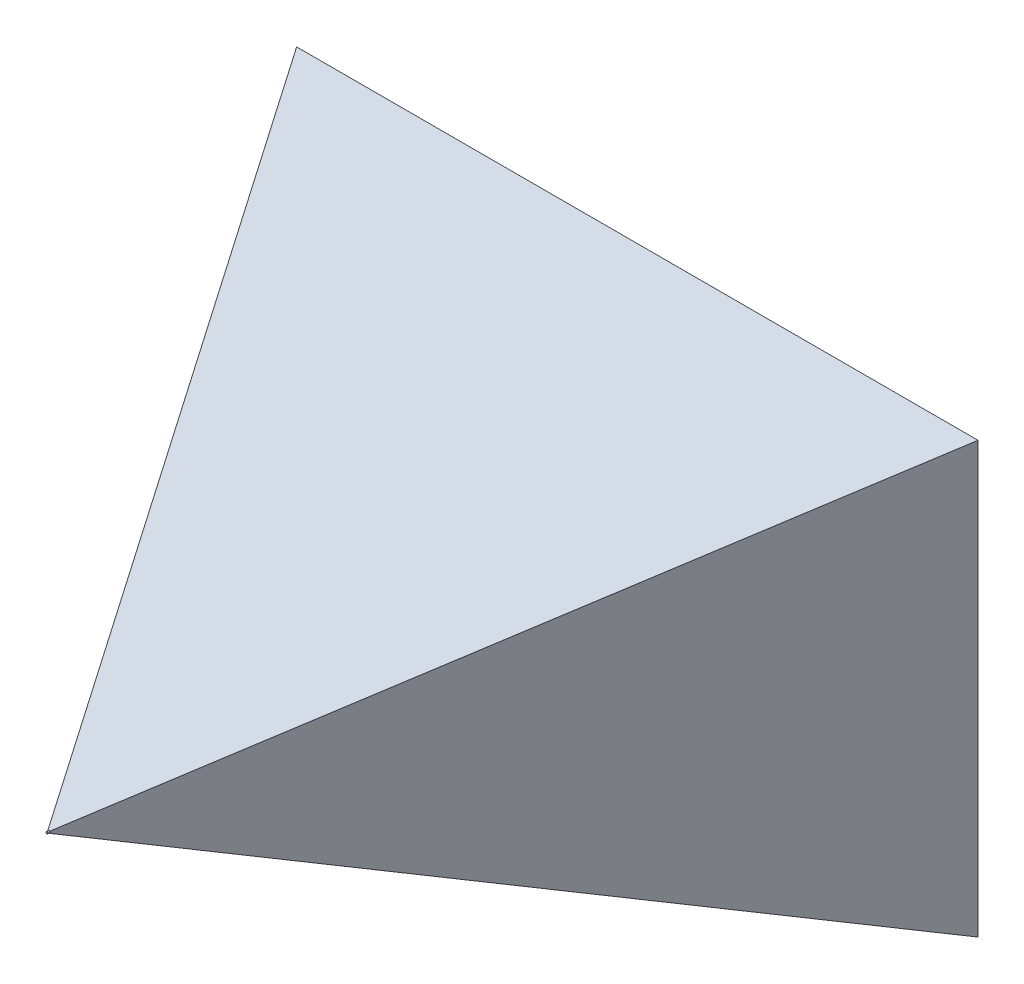
SolidWorks part; units mm, degrees
ref_plane "Front Plane" through (0, 0, 0) normal (0, 0, 1) x (1, 0, 0)
ref_plane "Top Plane" through (0, 0, 0) normal (0, 1, 0) x (1, 0, 0)
ref_plane "Right Plane" through (0, 0, 0) normal (1, 0, 0) x (0, 0, -1)
sketch "Sketch1" plane through (0, 0, 0) normal (0, 0, 1) x (1, 0, 0)
  line L1 (0, 0) -> (800, 0)
  line L2 (0, 0) -> (0, 800)
  line L3 (0, 800) -> (800, 800)
  line L4 (800, 0) -> (800, 800)
  dimension "D1" = 800
  dimension "D2" = 800
extrude "Boss-Extrude1" add sketch "Sketch1" along normal blind 600
sketch "Sketch2" plane through (800, 0, 0) normal (1, 0, 0) x (0, 0, -1)
  line L0 (-600, 800) -> (-600, 401)
  line L1 (-600, 0) -> (-600, 800) construction
  line L2 (-600, 401) -> (496.2435, 800)
  line L3 (-600, 800) -> (0, 800) construction
  line L4 (496.2435, 800) -> (-600, 800)
  line L6 (-600, 0) -> (0, 0) construction
  line L7 (496.2435, 0) -> (-600, 0)
  line L9 (-600, 0) -> (-600, 399)
  line L10 (-600, 399) -> (496.2435, 0)
  point P16 (-600, 400)
  dimension "D1" = 20
  dimension "D2" = 1
  dimension "D3" = 2
  dimension "D4" = 20
sketch "Sketch3" plane through (0, 0, 0) normal (0, -1, 0) x (1, 0, 0)
  line L0 (401, 600) -> (800, -91.0883)
  line L2 (800, -496.2435) -> (800, 600) construction
  line L3 (800, -91.0883) -> (800, 600)
  line L4 (800, 600) -> (401, 600)
  line L6 (0, 600) -> (0, -91.0883)
  line L7 (0, 600) -> (0, 0) construction
  line L9 (0, 600) -> (800, 600) construction
  line L10 (399, 600) -> (0, 600)
  line L11 (0, -91.0883) -> (399, 600)
  dimension "D1" = 2
  dimension "D2" = 30
  dimension "D3" = 401
  dimension "D4" = 30
sketch "Sketch4" plane through (0, 0, 600) normal (0, 0, 1) x (1, 0, 0)
  line L1 (0, 800) -> (800, 0) construction
  line L5 (800, 800) -> (0, 0) construction
  line L9 (800, 800) -> (800, 401) construction
  circle A0 centre (400, 400) radius 1
  point P17 (400, 400)
  dimension "D1" = 2
extrude "Cut-Extrude1" cut sketch "Sketch2" against normal through all
extrude "Cut-Extrude2" cut sketch "Sketch3" against normal through all
extrude "Boss-Extrude2" add sketch "Sketch4" along normal blind 2
